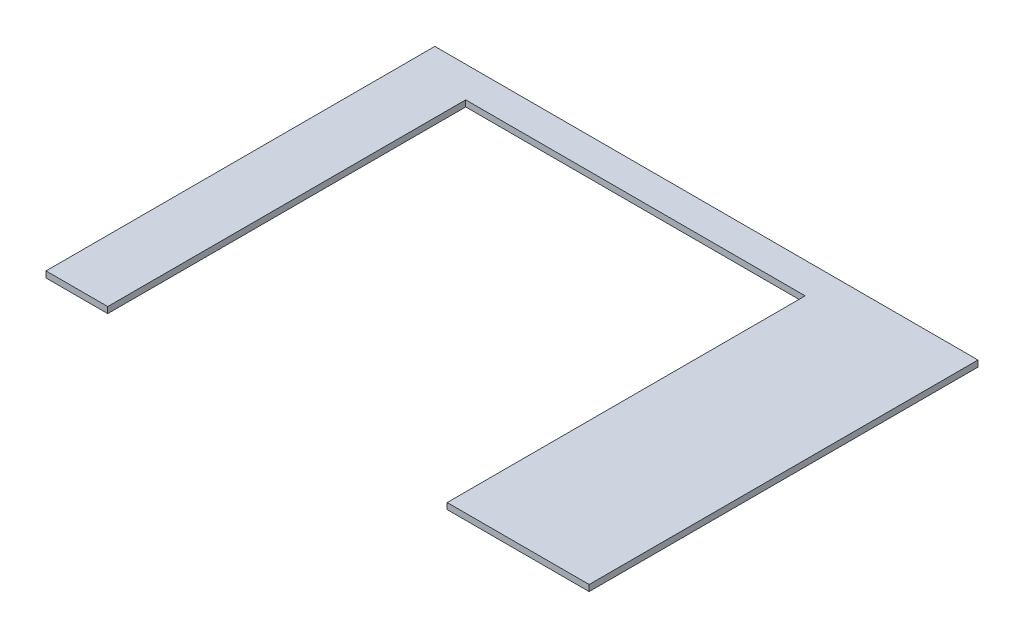
SolidWorks part; units mm, degrees
ref_plane "Спереди" through (0, 0, 0) normal (0, 0, 1) x (1, 0, 0)
ref_plane "Сверху" through (0, 0, 0) normal (0, 1, 0) x (1, 0, 0)
ref_plane "Справа" through (0, 0, 0) normal (1, 0, 0) x (0, 0, -1)
sketch "Эскиз1" plane through (0, 0, 0) normal (0, 1, 0) x (1, 0, 0)
  line L0 (100, 0) -> (100, 580)
  line L1 (100, 0) -> (0, 0)
  line L2 (0, 0) -> (0, 630)
  line L3 (0, 630) -> (880, 630)
  line L4 (880, 0) -> (880, 630)
  line L5 (100, 580) -> (650, 580)
  line L6 (650, 580) -> (650, 0)
  line L7 (650, 0) -> (880, 0)
  dimension "D1" = 100
  dimension "D2" = 880
  dimension "D3" = 50
  dimension "D4" = 230
  dimension "D5" = 630
  dimension "D6" = 630
extrude "Бобышка-Вытянуть1" add sketch "Эскиз1" along normal blind 10
